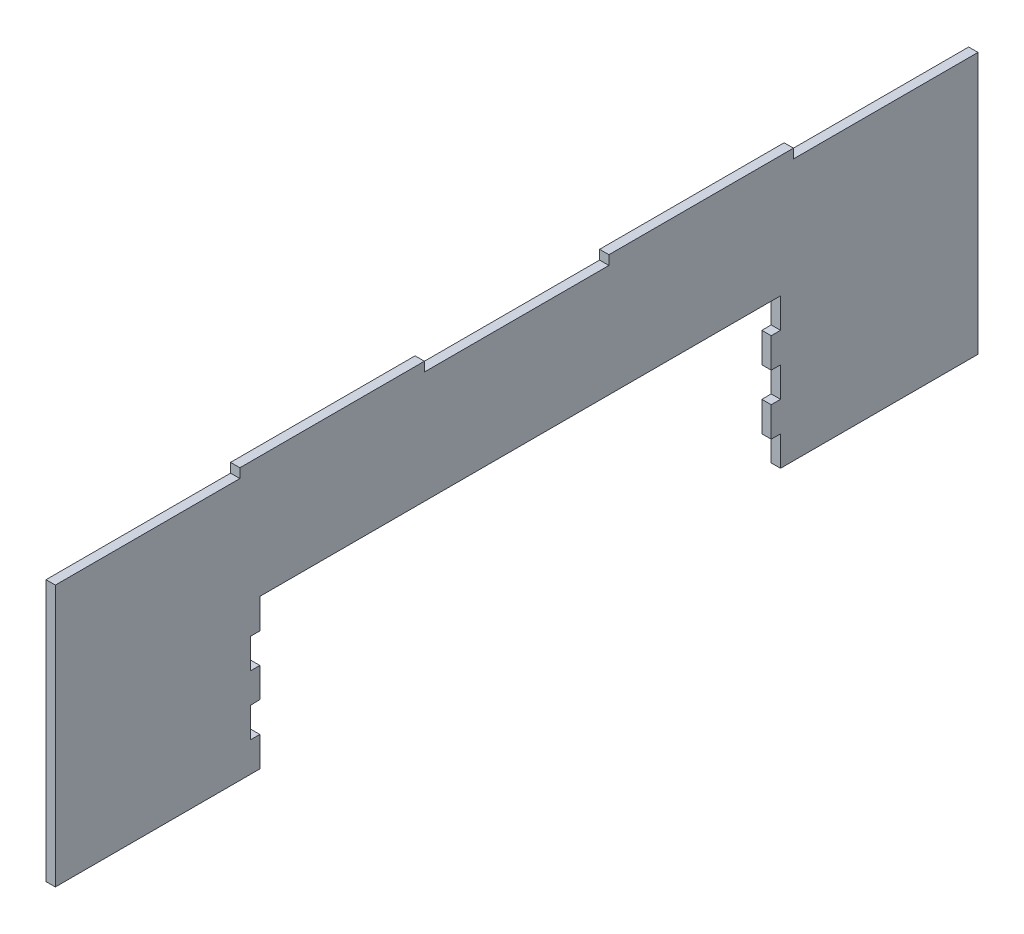
SolidWorks part; units mm, degrees
ref_plane "Front Plane" through (0, 0, 0) normal (0, 0, 1) x (1, 0, 0)
ref_plane "Top Plane" through (0, 0, 0) normal (0, 1, 0) x (1, 0, 0)
ref_plane "Right Plane" through (0, 0, 0) normal (1, 0, 0) x (0, 0, -1)
sketch "Sketch1" plane through (0, 0, 0) normal (1, 0, 0) x (0, 0, -1)
  line L0 (-247, 67.5) -> (-148.2, 67.5)
  line L2 (-247, 67.5) -> (-247, -72.5)
  line L3 (-247, -72.5) -> (-137.5, -72.5)
  line L4 (247, 67.5) -> (247, -72.5)
  line L7 (-148.2, 72.5) -> (-49.4, 72.5)
  line L9 (49.4, 72.5) -> (148.2, 72.5)
  line L11 (-148.2, 72.5) -> (-148.2, 67.5)
  line L12 (-49.4, 72.5) -> (-49.4, 67.5)
  line L13 (49.4, 72.5) -> (49.4, 67.5)
  line L14 (148.2, 72.5) -> (148.2, 67.5)
  line L15 (-49.4, 67.5) -> (49.4, 67.5)
  line L16 (148.2, 67.5) -> (247, 67.5)
  line L17 (-137.5, -72.5) -> (-137.5, -56.5)
  line L18 (0, 7.5) -> (-137.5, 7.5)
  line L19 (-137.5, -40.3593) -> (-137.5, -24.5)
  line L20 (0, 7.5) -> (141.2627, 7.5)
  line L21 (141.2627, 7.5) -> (141.2627, -8.5)
  line L24 (141.2627, -72.5) -> (247, -72.5)
  line L25 (-142.5, -8.5) -> (-142.5, -24.5)
  line L26 (-137.5, -8.5) -> (-137.5, 7.5)
  line L27 (-142.5, -40.5) -> (-142.5, -56.5)
  line L29 (141.2627, -24.5) -> (141.2627, -40.5)
  line L31 (141.2627, -56.5) -> (141.2627, -72.5)
  line L33 (136.2627, -56.5) -> (136.2627, -40.5)
  line L35 (136.2627, -24.5) -> (136.2627, -8.5)
  line L37 (-142.5, -8.5) -> (-137.5, -8.5)
  line L38 (-142.5, -24.5) -> (-137.5, -24.5)
  line L39 (-142.5, -40.5) -> (-137.5, -40.3593)
  line L40 (-142.5, -56.5) -> (-137.5, -56.5)
  line L45 (136.2627, -8.5) -> (141.2627, -8.5)
  line L46 (136.2627, -24.5) -> (141.2627, -24.5)
  line L47 (136.2627, -40.5) -> (141.2627, -40.5)
  line L48 (136.2627, -56.5) -> (141.2627, -56.5)
  point P0 (0, 0)
extrude "Boss-Extrude1" add sketch "Sketch1" along normal blind 5
